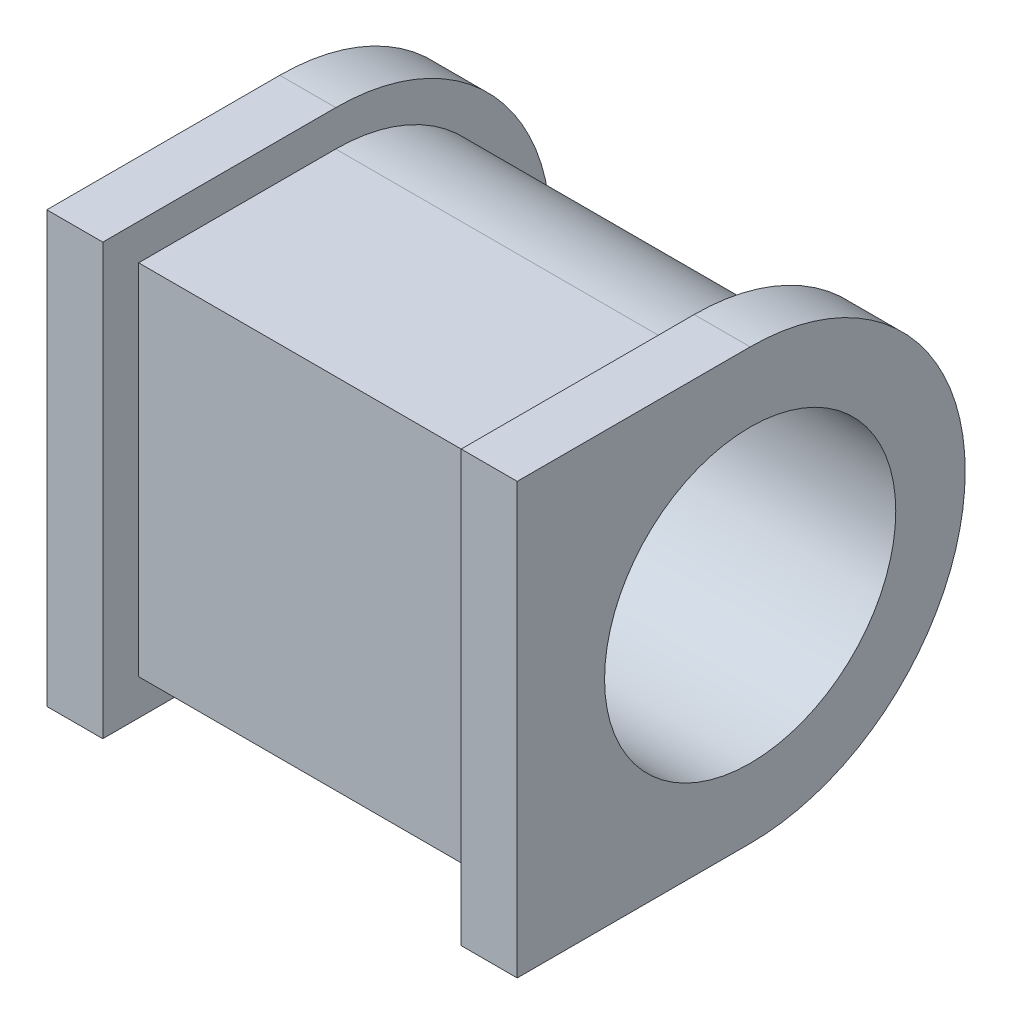
SolidWorks part; units mm, degrees
ref_plane "Front Plane" through (0, 0, 0) normal (0, 0, 1) x (1, 0, 0)
ref_plane "Top Plane" through (0, 0, 0) normal (0, 1, 0) x (1, 0, 0)
ref_plane "Right Plane" through (0, 0, 0) normal (1, 0, 0) x (0, 0, -1)
sketch "Sketch1" plane through (0, 0, 0) normal (1, 0, 0) x (0, 0, -1)
  line L0 (0, 0) -> (0, -26.097) construction
  line L1 (-52, 48) -> (-52, -48)
  line L2 (0, 0) -> (28.1623, 0) construction
  line L3 (-52, 48) -> (0, 48)
  line L4 (-52, -48) -> (0, -48)
  circle A0 centre (0, 0) radius 32.5
  arc A1 (0, -48) -> (0, 48) centre (0, 0) ccw
  dimension "D1" = 65
  dimension "D5" = 48
  dimension "D2" = 52
  dimension "D3" = 96
  dimension "D4" = 48
extrude "Boss-Extrude1" add sketch "Sketch1" along normal blind 12.5
sketch "Sketch2" plane through (12.5, 0, 0) normal (1, 0, 0) x (0, 0, -1)
  line L6 (0, 40) -> (-44, 40)
  line L7 (-44, 40) -> (-44, -40)
  line L8 (-44, -40) -> (0, -40)
  line L9 (0, 40) -> (-44, 40)
  line L10 (-44, 40) -> (-44, -40)
  line L11 (-44, -40) -> (0, -40)
  circle A1 centre (0, 0) radius 32.5
  arc A2 (0, -40) -> (0, 40) centre (0, 0) ccw
  arc A3 (0, -40) -> (0, 40) centre (0, 0) ccw
  dimension "D1" = 8
extrude "Boss-Extrude2" add sketch "Sketch2" along normal blind 80
sketch "Sketch3" plane through (92.5, 0, 0) normal (1, 0, 0) x (0, 0, -1)
  line L6 (0, 48) -> (-52, 48)
  line L7 (-52, 48) -> (-52, -48)
  line L8 (-52, -48) -> (0, -48)
  line L9 (0, 48) -> (-52, 48)
  line L10 (-52, 48) -> (-52, -48)
  line L11 (-52, -48) -> (0, -48)
  circle A1 centre (0, 0) radius 32.5
  arc A2 (0, -48) -> (0, 48) centre (0, 0) ccw
  arc A3 (0, -48) -> (0, 48) centre (0, 0) ccw
  dimension "D1" = 8
extrude "Boss-Extrude3" add sketch "Sketch3" along normal blind 12.5
